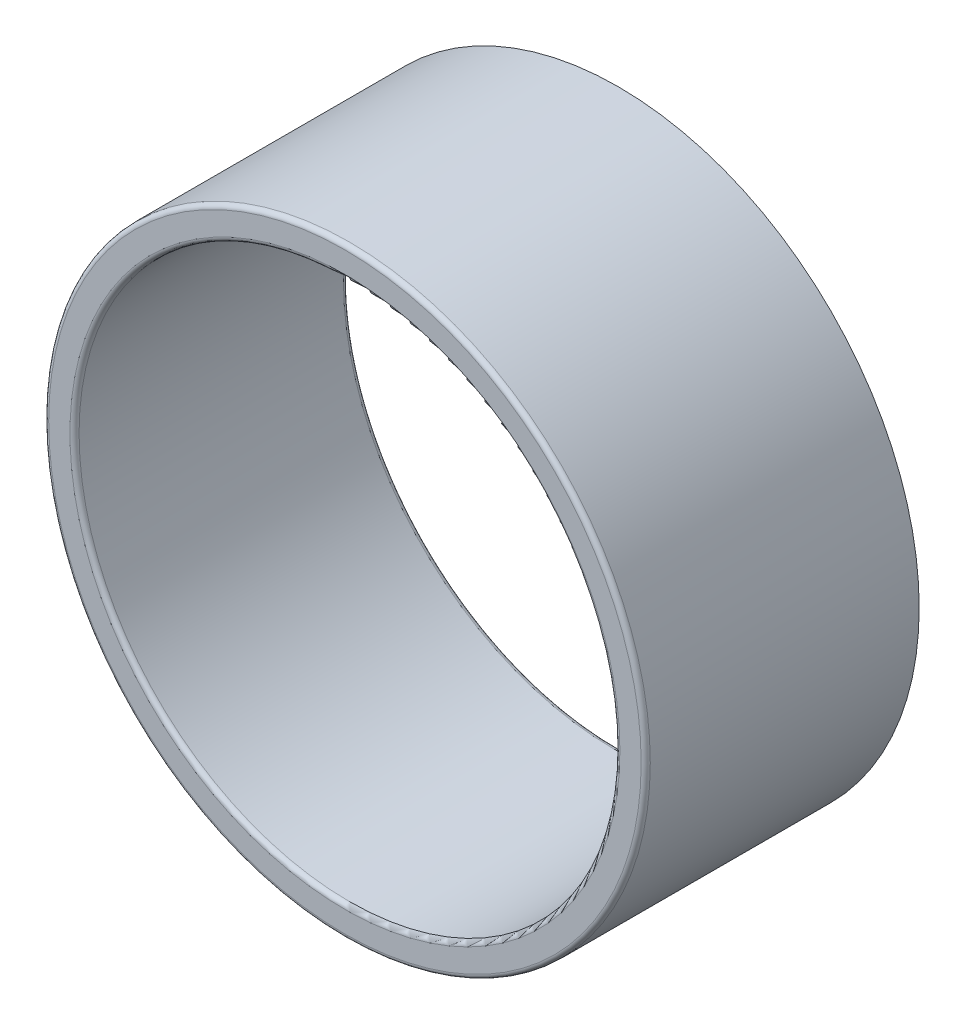
SolidWorks part; units mm, degrees
material "POLYURETHANE (11671)"
ref_plane "Front Plane" through (0, 0, 0) normal (0, 0, 1) x (1, 0, 0)
ref_plane "Top Plane" through (0, 0, 0) normal (0, 1, 0) x (1, 0, 0)
ref_plane "Right Plane" through (0, 0, 0) normal (1, 0, 0) x (0, 0, -1)
sketch "Sketch1" plane through (0, 0, 0) normal (0, 0, 1) x (1, 0, 0)
  circle A0 centre (232.735, 15) radius 89
  circle A1 centre (232.735, 15) radius 80 construction
  circle A2 centre (232.735, 15) radius 99
  dimension "D1" = 178
  dimension "D2" = 10
extrude "Boss-Extrude1" add sketch "Sketch1" against normal blind 90
fillet "Fillet1" radius 1.5 3 edges at (331.735, 15, 0) (321.735, 15, -90) (321.735, 15, 0)
